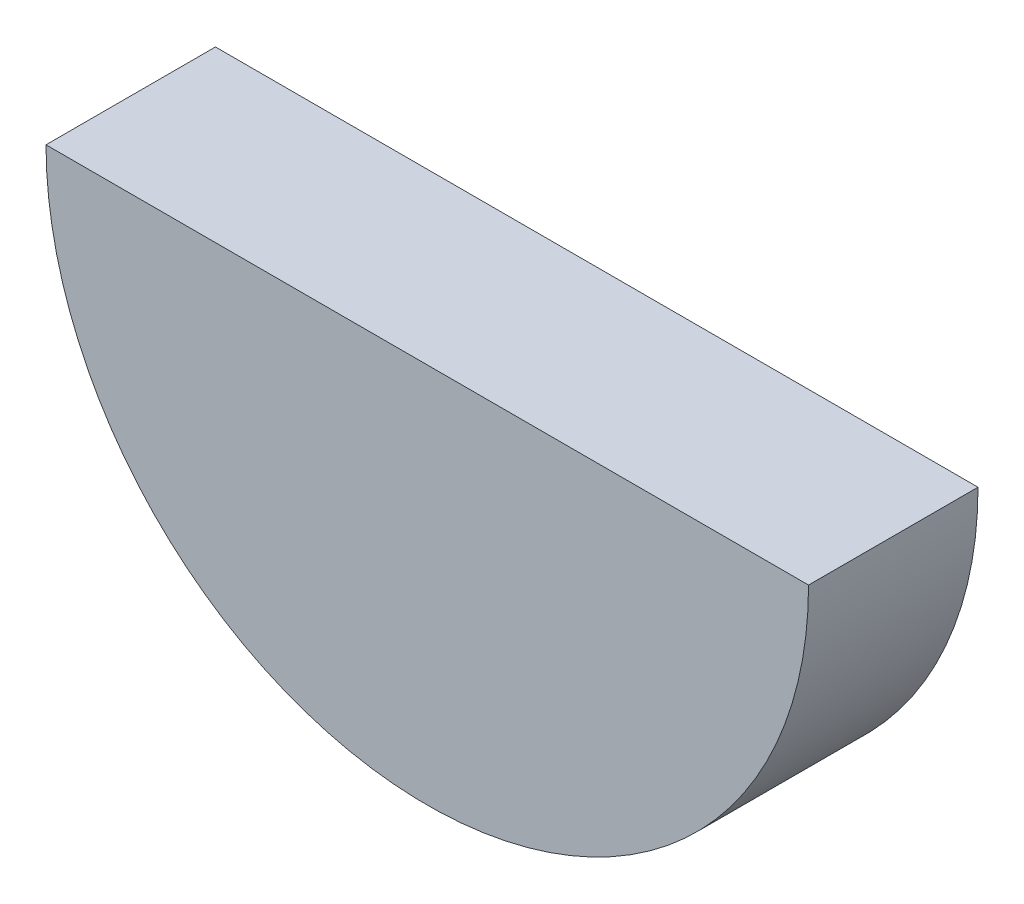
SolidWorks part; units mm, degrees
ref_plane "Front Plane" through (0, 0, 0) normal (0, 0, 1) x (1, 0, 0)
ref_plane "Top Plane" through (0, 0, 0) normal (0, 1, 0) x (1, 0, 0)
ref_plane "Right Plane" through (0, 0, 0) normal (1, 0, 0) x (0, 0, -1)
sketch "Sketch4" plane through (0, 0, 0) normal (0, 0, 1) x (1, 0, 0)
  line L0 (57.15, 0) -> (-57.15, 0) construction
  line L1 (-57.15, 0) -> (57.15, 0)
  arc A0 (-57.15, 0) -> (57.15, 0) centre (0, 0) ccw
  dimension "D1" = 114.3
extrude "Boss-Extrude1" add sketch "Sketch4" along normal blind 25.4
